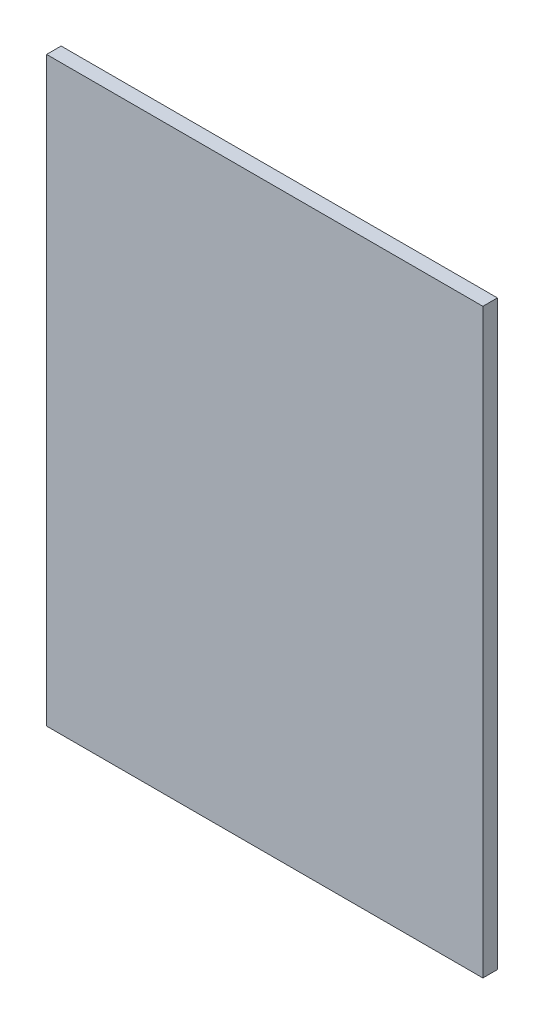
SolidWorks part; units mm, degrees
ref_plane "Front Plane" through (0, 0, 0) normal (0, 0, 1) x (1, 0, 0)
ref_plane "Top Plane" through (0, 0, 0) normal (0, 1, 0) x (1, 0, 0)
ref_plane "Right Plane" through (0, 0, 0) normal (1, 0, 0) x (0, 0, -1)
sketch "Sketch1" plane through (0, 0, 0) normal (0, 0, 1) x (1, 0, 0)
  line L1 (0, 0) -> (300, 0)
  line L2 (0, 0) -> (0, 400)
  line L3 (0, 400) -> (300, 400)
  line L4 (300, 0) -> (300, 400)
  dimension "D1" = 300
  dimension "D2" = 400
extrude "Extrude1" add sketch "Sketch1" along normal blind 10
